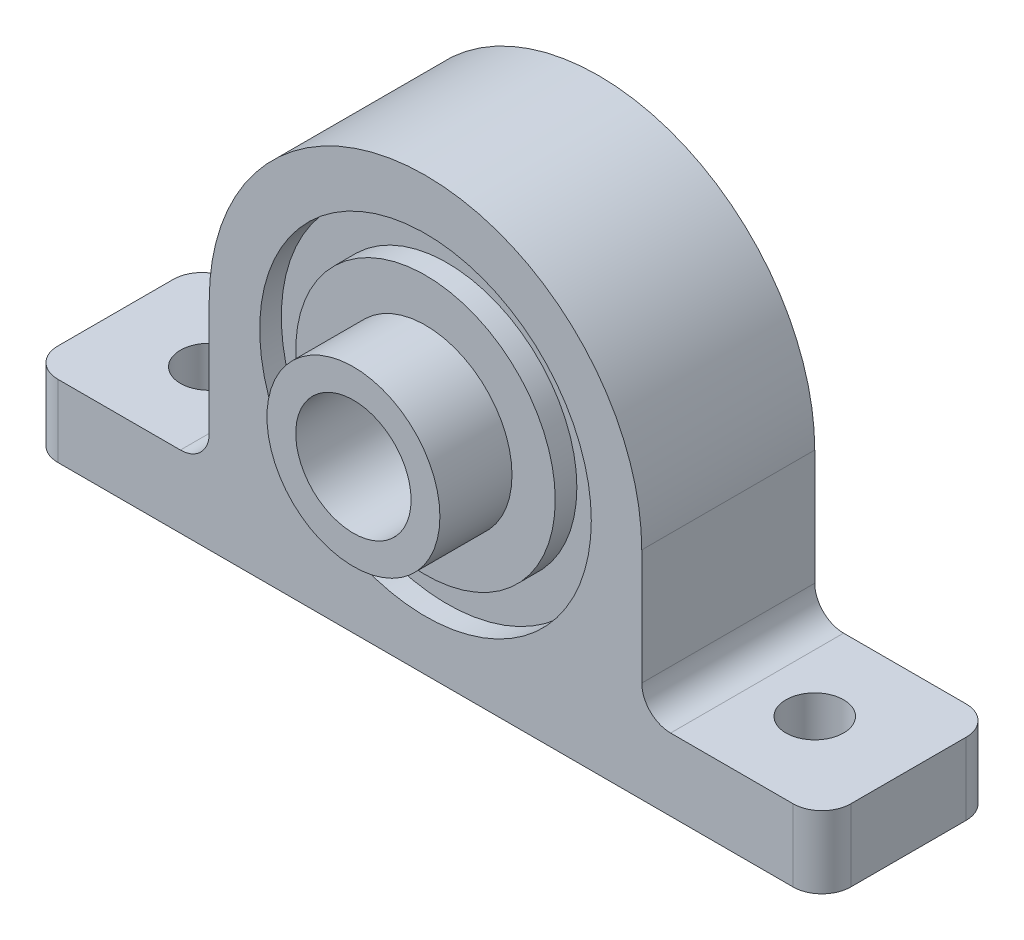
SolidWorks part; units mm, degrees
ref_plane "前视基准面" through (0, 0, 0) normal (0, 0, 1) x (1, 0, 0)
ref_plane "上视基准面" through (0, 0, 0) normal (0, 1, 0) x (1, 0, 0)
ref_plane "右视基准面" through (0, 0, 0) normal (1, 0, 0) x (0, 0, -1)
sketch "草图2" plane through (0, 0, 0) normal (0, 0, 1) x (1, 0, 0)
  line L0 (0, -15) -> (0, 15) construction
  line L1 (0, -15) -> (-21, -15) construction
  line L2 (0, -15) -> (21, -15) construction
  line L3 (0, -15) -> (-27.5, -15)
  line L4 (0, -15) -> (27.5, -15)
  line L5 (-27.5, -15) -> (-27.5, -10)
  line L6 (-27.5, -10) -> (-17, -10)
  line L7 (27.5, -10) -> (27.5, -15)
  line L8 (-15, 0) -> (-15, -8)
  line L9 (15, 0) -> (15, -8)
  line L10 (17, -10) -> (27.5, -10)
  circle A0 centre (0, 0) radius 4
  arc A1 (15, 0) -> (-15, 0) centre (0, 0) ccw
  arc A2 (15, -8) -> (17, -10) centre (17, -8) ccw
  arc A3 (-17, -10) -> (-15, -8) centre (-17, -8) ccw
  point P17 (15, -10)
  dimension "D1" = 2
extrude "凸台-拉伸1" add sketch "草图2" along normal blind 12
fillet "圆角1" radius 2 4 edges at (27.5, -12.5, 12) (27.5, -12.5, 0) (-27.5, -12.5, 0) (-27.5, -12.5, 12)
sketch "草图3" plane through (0, -10, 0) normal (0, 1, 0) x (1, 0, 0)
  line L0 (-27.5, -6) -> (27.5, -6) construction
  line L1 (-27.5, -10) -> (-27.5, -2) construction
  line L2 (27.5, -10) -> (27.5, -2) construction
  circle A0 centre (-21, -6) radius 2
  circle A1 centre (21, -6) radius 2
  point P10 (0, -6)
  dimension "D1" = 21
  dimension "D2" = 21
extrude "切除-拉伸1" cut sketch "草图3" against normal through all
ref_plane "基准面1" through (0, 0, 6) normal (0, 0, 1) x (1, 0, 0)
sketch "草图4" plane through (0, 0, 12) normal (0, 0, 1) x (1, 0, 0)
  circle A0 centre (0, 0) radius 6
  circle A1 centre (0, 0) radius 4
extrude "凸台-拉伸2" add sketch "草图4" along normal blind 5
sketch "草图5" plane through (0, 0, 12) normal (0, 0, 1) x (1, 0, 0)
  circle A0 centre (0, 0) radius 9
  circle A1 centre (0, 0) radius 11.5
extrude "切除-拉伸2" cut sketch "草图5" against normal blind 1.5
mirror "镜向1" about plane through (0, 0, 6) normal (0, 0, 1) of "切除-拉伸2"
